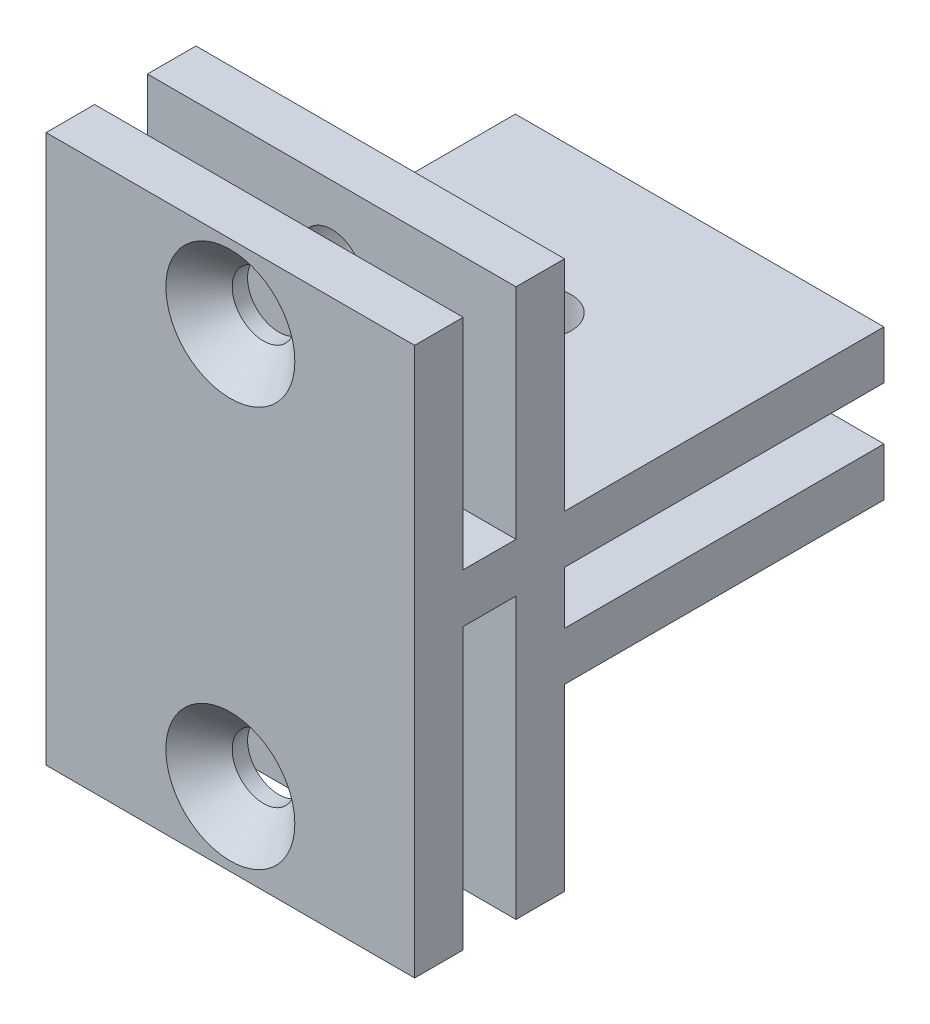
SolidWorks part; units mm, degrees
ref_plane "Plan de face" through (0, 0, 0) normal (0, 0, 1) x (1, 0, 0)
ref_plane "Plan de dessus" through (0, 0, 0) normal (0, 1, 0) x (1, 0, 0)
ref_plane "Plan de droite" through (0, 0, 0) normal (1, 0, 0) x (0, 0, -1)
sketch "Esquisse1" plane through (0, 0, 0) normal (0, 0, 1) x (1, 0, 0)
  line L1 (-41.0854, 37.2864) -> (-11.0854, 37.2864)
  line L2 (-41.0854, 37.2864) -> (-41.0854, -7.3136)
  line L3 (-41.0854, -7.3136) -> (-11.0854, -7.3136)
  line L4 (-11.0854, 37.2864) -> (-11.0854, -7.3136)
  dimension "D1" = 44.6
  dimension "D2" = 30
extrude "Boss.-Extru.1" add sketch "Esquisse1" along normal blind 12.2
sketch "Esquisse2" plane through (0, 37.2864, 0) normal (0, 1, 0) x (1, 0, 0)
  line L0 (-41.0854, -12.2) -> (-41.0854, 0) construction
  line L1 (-41.0854, -3.95) -> (-11.0854, -3.95)
  line L2 (-41.0854, -3.95) -> (-41.0854, -8.25)
  line L3 (-41.0854, -8.25) -> (-11.0854, -8.25)
  line L4 (-11.0854, -3.95) -> (-11.0854, -8.25)
  line L5 (-11.0854, -12.2) -> (-11.0854, 0) construction
  line L6 (-11.0854, 0) -> (-41.0854, 0) construction
  line L7 (-11.0854, -12.2) -> (-41.0854, -12.2) construction
  dimension "D1" = 3.95
  dimension "D2" = 3.95
  dimension "D3" = 4.3
extrude "Enlèv. mat.-Extru.1" cut sketch "Esquisse2" against normal blind 17.8
sketch "Esquisse3" plane through (0, -7.3136, 0) normal (0, -1, 0) x (1, 0, 0)
  line L0 (-11.0854, 12.2) -> (-11.0854, 0) construction
  line L1 (-11.0854, 3.95) -> (-41.0854, 3.95)
  line L2 (-11.0854, 3.95) -> (-11.0854, 8.25)
  line L3 (-11.0854, 8.25) -> (-41.0854, 8.25)
  line L4 (-41.0854, 3.95) -> (-41.0854, 8.25)
  line L5 (-41.0854, 12.2) -> (-41.0854, 0) construction
  line L6 (-41.0854, 0) -> (-11.0854, 0) construction
  dimension "D1" = 4.3
  dimension "D2" = 3.95
extrude "Enlèv. mat.-Extru.2" cut sketch "Esquisse3" against normal blind 22.8
sketch "Esquisse4" plane through (0, 0, 12.2) normal (0, 0, 1) x (1, 0, 0)
  line L0 (-41.0854, -7.3136) -> (-11.0854, -7.3136) construction
  line L1 (-41.0854, 37.2864) -> (-41.0854, -7.3136) construction
  line L2 (-11.0854, 37.2864) -> (-41.0854, 37.2864) construction
  line L3 (-11.0854, -7.3136) -> (-11.0854, 37.2864) construction
  circle A0 centre (-26.0854, -1.3136) radius 5.25
  circle A1 centre (-26.0854, 31.2864) radius 5.25
  dimension "D1" = 10.5
  dimension "D6" = 10.5
  dimension "D2" = 6
  dimension "D3" = 15
  dimension "D4" = 6
  dimension "D5" = 15
hole_wizard "Fraisage pour vis à tête fraisée bombée #51" positions "Esquisse3D1" profile "Esquisse5" countersink size "#5" standard "Ansi Inch" end condition through all
sketch3d "Esquisse3D1"
  point P0 (-26.0854, -1.3136, 12.2)
  point P3 (-26.0854, 31.2864, 12.2)
sketch "Esquisse5" plane through (-26.0854, -1.3136, 12.2) normal (1, 0, 0) x (0, -1, 0)
  line L0 (0, 0) -> (0, 12.2)
  line L1 (0, 12.2) -> (2.55, 12.2)
  line L2 (2.55, 12.2) -> (2.55, 2.7)
  line L3 (2.55, 2.7) -> (5.25, 0)
  line L5 (5.25, 0) -> (0, 0)
  line L6 (-2.55, 2.7) -> (-5.25, 0) construction
  line L11 (0, -6.35) -> (0, 107.95) construction
  dimension "Diamètre du perçage jusqu'au prochain" = 5.1
  dimension "Profondeur du perçage jusqu'au prochain" = 12.2
  dimension "Diamètre du fraisage entrant" = 10.5
  dimension "Angle du fraisage entrant" = 90
sketch "Esquisse6" plane through (0, 0, 0) normal (0, 0, -1) x (-1, 0, 0)
  line L0 (41.0854, 37.2864) -> (41.0854, -7.3136) construction
  line L1 (41.0854, 19.4864) -> (11.0854, 19.4864)
  line L2 (41.0854, 19.4864) -> (41.0854, 7.2864)
  line L3 (41.0854, 7.2864) -> (11.0854, 7.2864)
  line L4 (11.0854, 19.4864) -> (11.0854, 7.2864)
  line L5 (11.0854, -7.3136) -> (11.0854, 37.2864) construction
  line L8 (11.0854, 37.2864) -> (41.0854, 37.2864) construction
  dimension "D1" = 12.2
  dimension "D2" = 17.8
extrude "Boss.-Extru.2" add sketch "Esquisse6" along normal blind 26
sketch "Esquisse7" plane through (-41.0854, 0, 0) normal (-1, 0, 0) x (0, 0, 1)
  line L0 (-26, 7.2864) -> (-26, 19.4864) construction
  line L1 (-26, 11.2364) -> (0, 11.2364)
  line L2 (-26, 11.2364) -> (-26, 15.5364)
  line L3 (-26, 15.5364) -> (0, 15.5364)
  line L4 (0, 11.2364) -> (0, 15.5364)
  line L5 (-26, 19.4864) -> (0, 19.4864) construction
  line L6 (3.95, 15.4864) -> (3.95, -7.3136) construction
  dimension "D1" = 3.95
  dimension "D2" = 4.3
  dimension "D3" = 3.95
extrude "Enlèv. mat.-Extru.3" cut sketch "Esquisse7" against normal through all
sketch "Esquisse8" plane through (0, 7.2864, 0) normal (0, -1, 0) x (1, 0, 0)
  line L0 (-11.0854, -26) -> (-41.0854, -26) construction
  line L2 (-11.0854, -26) -> (-11.0854, 0) construction
  circle A0 centre (-26.0854, -13) radius 5.25
  dimension "D1" = 10.5
  dimension "D2" = 13
  dimension "D3" = 15
hole_wizard "Fraisage pour vis à tête fraisée bombée #52" positions "Esquisse3D2" profile "Esquisse9" countersink size "#5" standard "Ansi Inch" end condition through all
sketch3d "Esquisse3D2"
  point P0 (-26.0854, 7.2864, -13)
sketch "Esquisse9" plane through (-26.0854, 7.2864, -13) normal (1, 0, 0) x (0, 0, -1)
  line L0 (0, 0) -> (0, 30)
  line L1 (0, 30) -> (2.55, 30)
  line L2 (2.55, 30) -> (2.55, 2.7)
  line L3 (2.55, 2.7) -> (5.25, 0)
  line L5 (5.25, 0) -> (0, 0)
  line L6 (-2.55, 2.7) -> (-5.25, 0) construction
  line L11 (0, -6.35) -> (0, 107.95) construction
  dimension "Diamètre du perçage jusqu'au prochain" = 5.1
  dimension "Profondeur du perçage jusqu'au prochain" = 30
  dimension "Diamètre du fraisage entrant" = 10.5
  dimension "Angle du fraisage entrant" = 90
